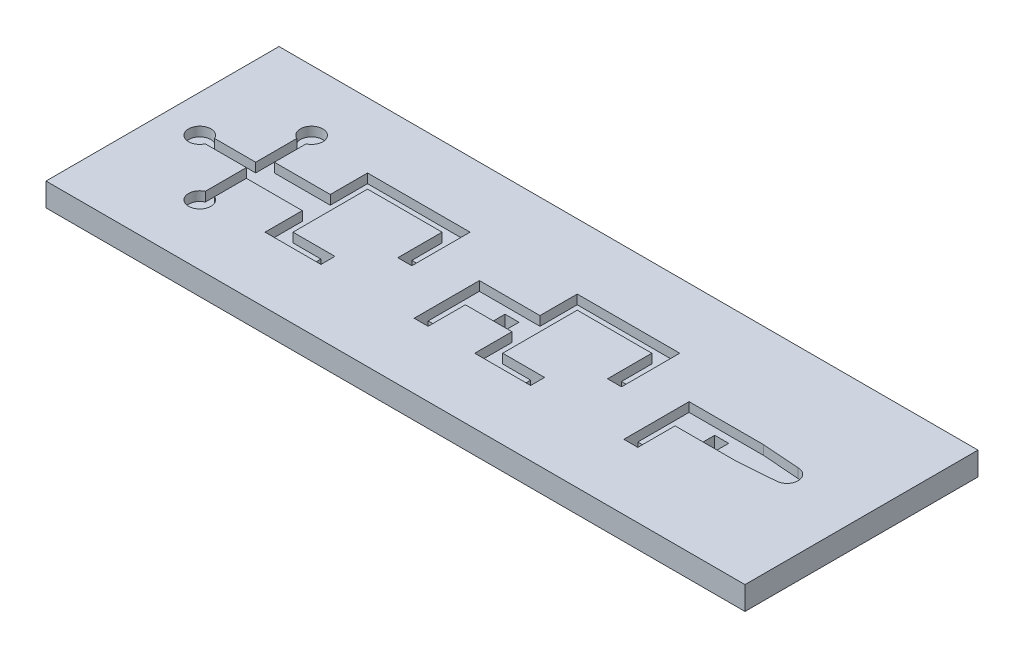
SolidWorks part; units mm, degrees
ref_plane "Front Plane" through (0, 0, 0) normal (0, 0, 1) x (1, 0, 0)
ref_plane "Top Plane" through (0, 0, 0) normal (0, 1, 0) x (1, 0, 0)
ref_plane "Right Plane" through (0, 0, 0) normal (1, 0, 0) x (0, 0, -1)
sketch "Sketch2" plane through (0, 0, 0) normal (0, 1, 0) x (1, 0, 0)
  line L1 (-29.0857, 8.3134) -> (45.9143, 8.3134)
  line L2 (-29.0857, 8.3134) -> (-29.0857, -16.6866)
  line L3 (-29.0857, -16.6866) -> (45.9143, -16.6866)
  line L4 (45.9143, 8.3134) -> (45.9143, -16.6866)
  line L5 (-29.0857, 8.3134) -> (45.9143, -16.6866) construction
  line L6 (-29.0857, -16.6866) -> (45.9143, 8.3134) construction
  point P0 (8.4143, -4.1866)
  dimension "D1" = 75
  dimension "D2" = 25
extrude "Boss-Extrude1" add sketch "Sketch2" against normal blind 2.5
sketch "Sketch1" plane through (0, 0, 0) normal (0, 1, 0) x (1, 0, 0)
  line L0 (-19.0857, -2.6866) -> (-19.0857, -5.6866)
  line L1 (-19.0857, -5.6866) -> (-11.0857, -5.6866)
  line L2 (-19.0857, -2.6866) -> (-11.0857, -2.6866)
  line L3 (3.4143, -2.6866) -> (3.4143, -5.6866)
  line L4 (-11.0857, 1.3134) -> (-3.0857, 1.3134)
  line L5 (3.4143, -5.6866) -> (11.4143, -5.6866)
  line L6 (3.4143, -2.6866) -> (11.4143, -2.6866)
  line L7 (-11.0857, 1.3134) -> (-11.0857, -0.1866)
  line L8 (-11.0857, -0.1866) -> (-3.0857, -0.1866)
  line L9 (-3.0857, 1.3134) -> (-3.0857, -0.1866)
  line L10 (-29.0857, -4.1866) -> (-11.0857, -4.1866) construction
  line L11 (-11.0857, -9.6866) -> (-6.5857, -9.6866)
  line L12 (-11.0857, -9.6866) -> (-11.0857, -8.1866)
  line L13 (-11.0857, -8.1866) -> (-6.5857, -8.1866)
  line L14 (-6.5857, -9.6866) -> (-6.5857, -8.1866)
  line L15 (-29.0857, 8.3134) -> (-29.0857, -16.6866) construction
  line L16 (-3.0857, 1.3134) -> (-1.5857, 1.3134)
  line L17 (-3.0857, 1.3134) -> (-3.0857, -4.9366)
  line L19 (-3.0857, -4.9366) -> (-1.5857, -4.9366)
  line L20 (-1.5857, 1.3134) -> (-1.5857, -4.9366)
  line L21 (11.4143, 1.3134) -> (19.4143, 1.3134)
  line L22 (11.4143, 1.3134) -> (11.4143, -0.1866)
  line L23 (11.4143, -0.1866) -> (19.4143, -0.1866)
  line L24 (19.4143, 1.3134) -> (19.4143, -0.1866)
  line L25 (-1.5857, -4.1866) -> (11.4143, -4.1866) construction
  line L26 (11.4143, -9.6866) -> (15.9143, -9.6866)
  line L27 (11.4143, -9.6866) -> (11.4143, -8.1866)
  line L28 (11.4143, -8.1866) -> (15.9143, -8.1866)
  line L29 (15.9143, -9.6866) -> (15.9143, -8.1866)
  line L30 (19.4143, 1.3134) -> (20.9143, 1.3134)
  line L31 (19.4143, 1.3134) -> (19.4143, -4.9366)
  line L32 (19.4143, -4.9366) -> (20.9143, -4.9366)
  line L33 (20.9143, 1.3134) -> (20.9143, -4.9366)
  line L34 (11.4143, -2.6866) -> (11.4143, -5.6866)
  line L35 (11.4143, -5.6866) -> (9.9143, -5.6866)
  line L36 (11.4143, -5.6866) -> (11.4143, -9.6866)
  line L37 (11.4143, -9.6866) -> (9.9143, -9.6866)
  line L38 (9.9143, -5.6866) -> (9.9143, -9.6866)
  line L39 (11.4143, -2.6866) -> (9.9143, -2.6866)
  line L40 (11.4143, -2.6866) -> (11.4143, 1.3134)
  line L41 (11.4143, 1.3134) -> (9.9143, 1.3134)
  line L42 (9.9143, -2.6866) -> (9.9143, 1.3134)
  line L43 (25.9143, -2.6866) -> (25.9143, -5.6866)
  line L44 (3.4143, -5.6866) -> (4.9143, -5.6866)
  line L45 (3.4143, -5.6866) -> (3.4143, -9.6866)
  line L46 (3.4143, -9.6866) -> (4.9143, -9.6866)
  line L47 (-11.0857, -2.6866) -> (-11.0857, -5.6866)
  line L48 (4.9143, -5.6866) -> (4.9143, -9.6866)
  line L49 (25.9143, -5.6866) -> (33.9143, -5.6866)
  line L50 (25.9143, -2.6866) -> (33.9143, -2.6866)
  line L52 (25.9143, -5.6866) -> (27.4143, -5.6866)
  line L53 (25.9143, -5.6866) -> (25.9143, -9.6866)
  line L54 (25.9143, -9.6866) -> (27.4143, -9.6866)
  line L55 (20.9143, -4.1866) -> (33.9143, -4.1866) construction
  line L56 (27.4143, -5.6866) -> (27.4143, -9.6866)
  line L61 (-11.0857, -5.6866) -> (-12.5857, -5.6866)
  line L62 (-11.0857, -5.6866) -> (-11.0857, -9.6866)
  line L63 (-11.0857, -9.6866) -> (-12.5857, -9.6866)
  line L64 (-12.5857, -5.6866) -> (-12.5857, -9.6866)
  line L65 (-11.0857, -2.6866) -> (-12.5857, -2.6866)
  line L66 (-11.0857, -2.6866) -> (-11.0857, 1.3134)
  line L67 (-11.0857, 1.3134) -> (-12.5857, 1.3134)
  line L68 (-12.5857, -2.6866) -> (-12.5857, 1.3134)
  line L72 (33.9143, -2.6866) -> (33.9143, -5.6866)
  line L73 (33.9143, -5.6866) -> (32.4143, -5.6866)
  line L77 (33.9143, -2.6866) -> (32.4143, -2.6866)
  point P26 (-19.0857, -4.1866)
  point P31 (3.4143, -4.1866)
  point P56 (25.9143, -4.1866)
  dimension "D1" = 1.5
  dimension "D2" = 3
  dimension "D4" = 3
  dimension "D5" = 8
  dimension "D6" = 1.5
  dimension "D7" = 8
  dimension "D8" = 1.5
  dimension "D9" = 8
  dimension "D10" = 4
  dimension "D11" = 4
  dimension "D12" = 1.5
  dimension "D13" = 4.5
  dimension "D14" = 1.5
  dimension "D15" = 6.25
  dimension "D16" = 1.5
  dimension "D17" = 1.5
  dimension "D18" = 1.5
  dimension "D19" = 8
  dimension "D20" = 4
  dimension "D21" = 4
  dimension "D22" = 1.5
  dimension "D23" = 4.5
  dimension "D24" = 1.5
  dimension "D25" = 6.25
  dimension "D26" = 5
  dimension "D27" = 1.5
  dimension "D28" = 4
  dimension "D29" = 3
  dimension "D30" = 8
  dimension "D31" = 4
  dimension "D32" = 1.5
  dimension "D35" = 10
  dimension "D42" = 5
extrude "Cut-Extrude1" cut sketch "Sketch1" against normal blind 1
sketch "Sketch3" plane through (0, 0, 0) normal (0, 1, 0) x (1, 0, 0)
  line L0 (25.9143, -2.6866) -> (25.9143, -9.6866) construction
  line L1 (-6.5857, -9.6866) -> (-12.5857, -9.6866) construction
  line L2 (-6.5857, -8.1866) -> (-8.0857, -8.1866)
  line L3 (-6.5857, -8.1866) -> (-6.5857, -9.6866)
  line L4 (-6.5857, -9.6866) -> (-8.0857, -9.6866)
  line L6 (-8.0857, -8.1866) -> (-8.0857, -9.6866)
  line L7 (-1.5857, 1.3134) -> (-1.5857, -4.9366) construction
  line L8 (-3.0857, -4.9366) -> (-1.5857, -4.9366)
  line L9 (-3.0857, -4.9366) -> (-3.0857, -3.4366)
  line L11 (-3.0857, -3.4366) -> (-1.5857, -3.4366)
  line L12 (-1.5857, -4.9366) -> (-1.5857, -3.4366)
  line L13 (4.9143, -5.6866) -> (4.9143, -9.6866) construction
  line L14 (3.4143, -9.6866) -> (4.9143, -9.6866)
  line L16 (11.4143, -4.1866) -> (3.4143, -4.1866) construction
  line L17 (11.4143, -8.1866) -> (11.4143, -0.1866) construction
  line L18 (3.4143, -2.6866) -> (3.4143, -9.6866) construction
  line L19 (33.9143, -4.1866) -> (25.9143, -4.1866) construction
  line L21 (29.4143, -3.4366) -> (30.9143, -3.4366)
  line L22 (29.4143, -3.4366) -> (29.4143, -4.9366)
  line L23 (29.4143, -4.9366) -> (30.9143, -4.9366)
  line L24 (30.9143, -3.4366) -> (30.9143, -4.9366)
  line L26 (3.4143, -9.6866) -> (3.4143, -8.1866)
  line L27 (3.4143, -8.1866) -> (4.9143, -8.1866)
  line L28 (4.9143, -9.6866) -> (4.9143, -8.1866)
  line L29 (15.9143, -9.6866) -> (9.9143, -9.6866) construction
  line L30 (33.9143, -2.6866) -> (33.9143, -5.6866) construction
  line L31 (25.9143, -2.6866) -> (25.9143, -9.6866) construction
  line L35 (6.9143, -3.4366) -> (8.4143, -3.4366)
  line L40 (6.9143, -3.4366) -> (6.9143, -4.9366)
  line L41 (6.9143, -4.9366) -> (8.4143, -4.9366)
  line L42 (8.4143, -3.4366) -> (8.4143, -4.9366)
  line L43 (15.9143, -8.1866) -> (14.4143, -8.1866)
  line L44 (15.9143, -8.1866) -> (15.9143, -9.6866)
  line L45 (15.9143, -9.6866) -> (14.4143, -9.6866)
  line L46 (14.4143, -8.1866) -> (14.4143, -9.6866)
  line L47 (20.9143, 1.3134) -> (20.9143, -4.9366) construction
  line L48 (19.4143, -4.9366) -> (20.9143, -4.9366)
  line L49 (19.4143, -4.9366) -> (19.4143, -3.4366)
  line L50 (19.4143, -3.4366) -> (20.9143, -3.4366)
  line L51 (20.9143, -4.9366) -> (20.9143, -3.4366)
  line L52 (27.4143, -5.6866) -> (27.4143, -9.6866) construction
  line L53 (25.9143, -9.6866) -> (27.4143, -9.6866)
  line L54 (25.9143, -9.6866) -> (25.9143, -8.1866)
  line L55 (25.9143, -8.1866) -> (27.4143, -8.1866)
  line L56 (27.4143, -9.6866) -> (27.4143, -8.1866)
  point P28 (8.4143, -4.1866)
  point P29 (0, 0)
  point P30 (19.4143, -4.1866)
  point P34 (30.9143, -4.1866)
  point P43 (0, 0)
  point P46 (33.9143, -4.1866)
  point P47 (0, 0)
  point P50 (0, 0)
  point P51 (0, 0)
  point P52 (25.9143, -4.1866)
  dimension "D1" = 1.5
  dimension "D2" = 1.5
  dimension "D3" = 1.5
  dimension "D4" = 1.5
  dimension "D5" = 3.5
  dimension "D6" = 1.5
  dimension "D7" = 1.5
  dimension "D8" = 1.5
  dimension "D9" = 1.5
  dimension "D10" = 1.5
  dimension "D11" = 3.5
extrude "Cut-Extrude2" cut sketch "Sketch3" against normal through all
sketch "Sketch4" plane through (0, 0, 0) normal (0, 1, 0) x (1, 0, 0)
  line L0 (-25.0857, -4.1866) -> (-19.0857, -4.1866) construction
  line L1 (-29.0857, 8.3134) -> (-29.0857, -16.6866) construction
  line L3 (-25.0857, -4.6866) -> (-19.0857, -4.6866)
  line L4 (-19.0857, 1.8134) -> (-19.0857, -10.1866) construction
  line L5 (-19.5857, 1.8134) -> (-19.5857, -10.1866)
  line L6 (-18.5857, 1.8134) -> (-18.5857, -10.1866)
  line L7 (37.9143, -2.9866) -> (33.9143, -2.6866)
  line L8 (-25.0857, -3.6866) -> (-19.0857, -3.6866)
  line L9 (33.9143, -2.6866) -> (33.9143, -5.6866)
  line L10 (33.9143, -5.6866) -> (37.9143, -5.3866)
  arc A0 (37.9143, -5.3866) -> (37.9143, -2.9866) centre (37.9143, -4.1866) ccw
  circle A1 centre (-19.0857, -10.1866) radius 1.2
  circle A2 centre (-19.0857, 1.8134) radius 1.2
  circle A3 centre (-25.0857, -4.1866) radius 1.2
  arc A4 (-19.5857, 1.8134) -> (-18.5857, 1.8134) centre (-19.0857, 1.8134) cw
  arc A5 (-19.5857, -10.1866) -> (-18.5857, -10.1866) centre (-19.0857, -10.1866) ccw
  arc A6 (-25.0857, -4.6866) -> (-25.0857, -3.6866) centre (-25.0857, -4.1866) cw
  arc A7 (-19.0857, -4.6866) -> (-19.0857, -3.6866) centre (-19.0857, -4.1866) ccw
  point P1 (33.9143, -4.1866)
  point P8 (0, 0)
  point P21 (-19.0857, -4.1866)
  point P26 (-19.0857, -3.6279)
  point P27 (0, 0)
  point P30 (-29.0857, -4.1866)
  point P31 (0, 0)
  point P33 (0, 0)
  dimension "D1" = 2.4
  dimension "D6" = 6
  dimension "D7" = 12
  dimension "D8" = 4
  dimension "D2" = 0.5
  dimension "D3" = 0.5
  dimension "D4" = 0.5
  dimension "D5" = 0.5
extrude "Cut-Extrude3" cut sketch "Sketch4" against normal blind 1
